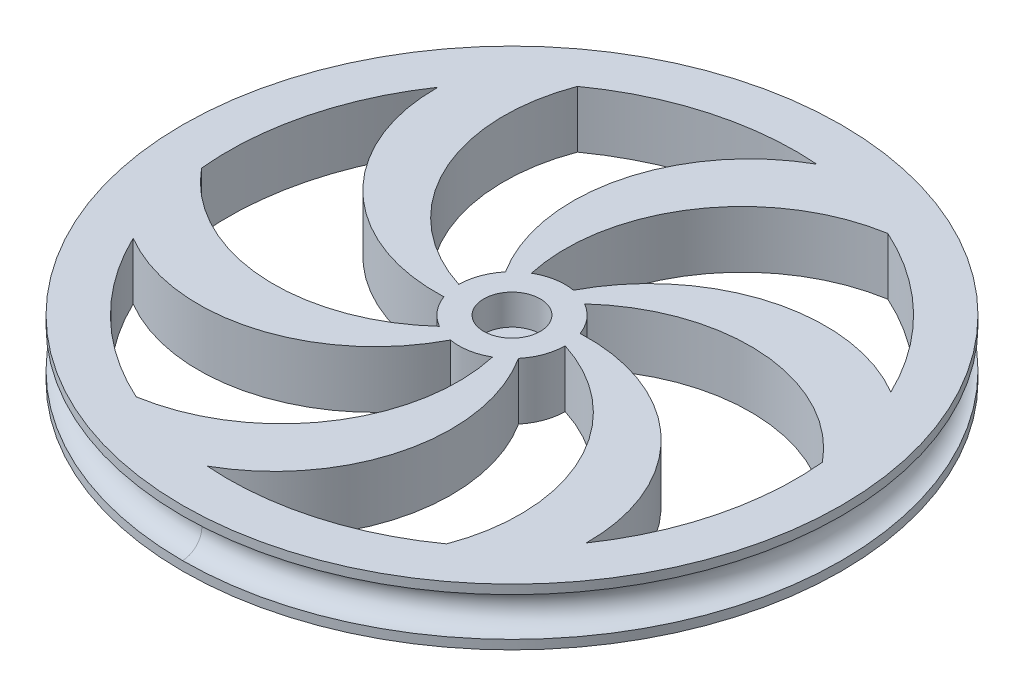
SolidWorks part; units mm, degrees
ref_plane "Front Plane" through (0, 0, 0) normal (0, 0, 1) x (1, 0, 0)
ref_plane "Top Plane" through (0, 0, 0) normal (0, 1, 0) x (1, 0, 0)
ref_plane "Right Plane" through (0, 0, 0) normal (1, 0, 0) x (0, 0, -1)
sketch "Sketch1" plane through (0, 0, 0) normal (0, 1, 0) x (1, 0, 0)
  circle A0 centre (0, 0) radius 27.559
  dimension "D1" = 55.118
extrude "Boss-Extrude1" add sketch "Sketch1" along normal blind 4.7625 contours A0
sketch "Sketch2" plane through (0, 0, 0) normal (0, 0, 1) x (1, 0, 0)
  line L0 (-27.559, 4.7625) -> (-27.559, 0) construction
  circle A0 centre (-27.559, 2.3812) radius 1.6192
  dimension "D1" = 3.2385
sweep "Cut-Sweep1" cut profiles "Sketch2" path edge at (0, 0, 27.559)
sketch "Sketch7" plane through (0, 4.7625, 0) normal (0, 1, 0) x (1, 0, 0)
  line L0 (4.445, 0) -> (14.097, 0) construction
  line L1 (14.097, 0) -> (23.749, 0) construction
  circle A0 centre (0, 0) radius 4.445
  circle A1 centre (0, 0) radius 23.749
  circle A2 centre (0, 0) radius 14.097 construction
  arc A3 (4.445, 0) -> (13.8337, -19.304) centre (0, -14.097) cw
  arc A4 (4.1769, 1.5203) -> (19.6018, -13.4084) centre (4.8215, -13.2468) cw
  arc A5 (3.4051, -2.8572) -> (-1.8112, -23.6798) centre (-9.0614, -10.7989) cw
  arc A6 (2.2225, -3.8495) -> (-9.8009, -21.6323) centre (-12.2084, -7.0485) cw
  arc A7 (-0.7719, -4.3775) -> (-21.4129, -10.2714) centre (-13.8828, 2.4479) cw
  arc A8 (-2.2225, -3.8495) -> (-23.6346, -2.3283) centre (-12.2084, 7.0485) cw
  arc A9 (-4.1769, -1.5203) -> (-19.6018, 13.4084) centre (-4.8215, 13.2468) cw
  arc A10 (-4.445, 0) -> (-13.8337, 19.304) centre (0, 14.097) cw
  arc A11 (-3.4051, 2.8572) -> (1.8112, 23.6798) centre (9.0614, 10.7989) cw
  arc A12 (-2.2225, 3.8495) -> (9.8009, 21.6323) centre (12.2084, 7.0485) cw
  arc A13 (0.7719, 4.3775) -> (21.4129, 10.2714) centre (13.8828, -2.4479) cw
  arc A14 (2.2225, 3.8495) -> (23.6346, 2.3283) centre (12.2084, -7.0485) cw
  circle A15 centre (0, 0) radius 27.559 construction
  point P45 (0, 0)
  dimension "D1" = 8.89
  dimension "D2" = 3.81
  dimension "D3" = 20
  dimension "D4" = 20
  dimension "D5" = 6
hole_wizard "#40 (0.098) Diameter Hole1" positions "3DSketch4" profile "Sketch8" hole size "#40" standard "ANSI Inch" end condition through all
sketch3d "3DSketch4"
  point P0 (0, 0, 0)
sketch "Sketch8" plane through (0, 0, 0) normal (1, 0, 0) x (0, 0, -1)
  line L0 (0, 0) -> (0, 4.7625)
  line L1 (0, 4.7625) -> (1.2446, 4.7625)
  line L2 (1.2446, 4.7625) -> (1.2446, 0)
  line L5 (1.2446, 0) -> (0, 0)
  line L11 (0, -6.35) -> (0, 107.95) construction
  dimension "Thru Hole Dia." = 2.4892
  dimension "Thru Hole Depth" = 4.7625
extrude "Cut-Extrude1" cut sketch "Sketch7" against normal through all contours A0 A13 A1 A12 | A14 A0 A4 A1 | A0 A5 A1 A3 | A0 A7 A1 A6 | A0 A9 A1 A8 | A0 A11 A1 A10
sketch "Sketch9" plane through (0, 4.7625, 0) normal (0, 1, 0) x (1, 0, 0)
  circle A0 centre (0, 0) radius 2.3622
extrude "Cut-Extrude2" cut sketch "Sketch9" against normal blind 2.54
